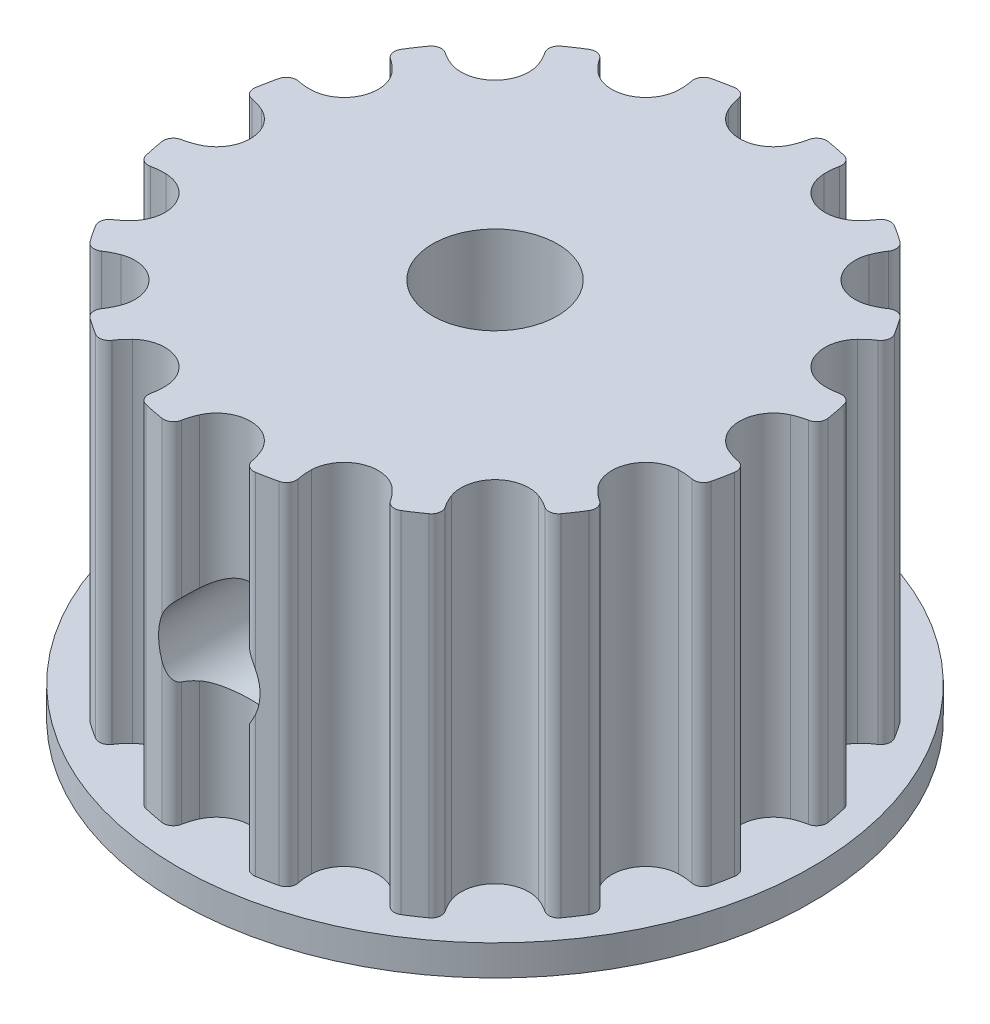
SolidWorks part; units mm, degrees
material "Alum Plate"
ref_plane "Front Plane" through (0, 0, 0) normal (0, 0, 1) x (1, 0, 0)
ref_plane "Top Plane" through (0, 0, 0) normal (0, 1, 0) x (1, 0, 0)
ref_plane "Right Plane" through (0, 0, 0) normal (1, 0, 0) x (0, 0, -1)
other "Bounding Box"
ref_plane "Default Plane" through (-8.9266, -12.7485, 0) normal (-0.1736, 0.9848, 0) x (0.9848, 0.1736, 0)
sketch "Sketch1" plane through (0, 0, 0) normal (0, 1, 0) x (1, 0, 0)
  line L0 (0, -7.8245) -> (0, 0) construction
  circle A0 centre (0, 0) radius 1.5625
  arc B0 (-1.8508, -6.777) -> (-1.6633, -7.0715) centre (-1.6061, -6.8282) ccw
  arc B1 (-1.6633, -7.0715) -> (-1.1695, -7.1697) centre (0, 0) ccw
  arc B2 (-1.1695, -7.1697) -> (-0.8836, -6.9694) centre (-1.1292, -6.923) ccw
  arc B3 (-0.7739, -6.6229) -> (-0.8836, -6.9694) centre (0.61, -7.2516) ccw
  arc B4 (0.7739, -6.6229) -> (-0.7739, -6.6229) centre (0, -6.9745) ccw
  arc B5 (0.8836, -6.9694) -> (0.7739, -6.6229) centre (-0.61, -7.2516) ccw
  arc B6 (0.8836, -6.9694) -> (1.1695, -7.1697) centre (1.1292, -6.923) ccw
  arc B7 (1.1695, -7.1697) -> (1.6633, -7.0715) centre (0, 0) ccw
  arc B8 (1.6633, -7.0715) -> (1.8508, -6.777) centre (1.6061, -6.8282) ccw
  arc B9 (1.8195, -6.4149) -> (1.8508, -6.777) centre (3.3386, -6.4662) ccw
  arc B10 (3.2495, -5.8226) -> (1.8195, -6.4149) centre (2.669, -6.4436) ccw
  arc B11 (3.4834, -6.1008) -> (3.2495, -5.8226) centre (2.2115, -6.9331) ccw
  arc B12 (3.4834, -6.1008) -> (3.8242, -6.1764) centre (3.6926, -5.9639) ccw
  arc B13 (3.8242, -6.1764) -> (4.2428, -5.8967) centre (0, 0) ccw
  arc B14 (4.2428, -5.8967) -> (4.3033, -5.5529) centre (4.0968, -5.6938) ccw
  arc B15 (4.1359, -5.2303) -> (4.3033, -5.5529) centre (5.559, -4.6963) ccw
  arc B16 (5.2303, -4.1359) -> (4.1359, -5.2303) centre (4.9317, -4.9317) ccw
  arc B17 (5.5529, -4.3033) -> (5.2303, -4.1359) centre (4.6963, -5.559) ccw
  arc B18 (5.5529, -4.3033) -> (5.8967, -4.2428) centre (5.6938, -4.0968) ccw
  arc B19 (5.8967, -4.2428) -> (6.1764, -3.8242) centre (0, 0) ccw
  arc B20 (6.1764, -3.8242) -> (6.1008, -3.4834) centre (5.9639, -3.6926) ccw
  arc B21 (5.8226, -3.2495) -> (6.1008, -3.4834) centre (6.9331, -2.2115) ccw
  arc B22 (6.4149, -1.8195) -> (5.8226, -3.2495) centre (6.4436, -2.669) ccw
  arc B23 (6.777, -1.8508) -> (6.4149, -1.8195) centre (6.4662, -3.3386) ccw
  arc B24 (6.777, -1.8508) -> (7.0715, -1.6633) centre (6.8282, -1.6061) ccw
  arc B25 (7.0715, -1.6633) -> (7.1697, -1.1695) centre (0, 0) ccw
  arc B26 (7.1697, -1.1695) -> (6.9694, -0.8836) centre (6.923, -1.1292) ccw
  arc B27 (6.6229, -0.7739) -> (6.9694, -0.8836) centre (7.2516, 0.61) ccw
  arc B28 (6.6229, 0.7739) -> (6.6229, -0.7739) centre (6.9745, 0) ccw
  arc B29 (6.9694, 0.8836) -> (6.6229, 0.7739) centre (7.2516, -0.61) ccw
  arc B30 (6.9694, 0.8836) -> (7.1697, 1.1695) centre (6.923, 1.1292) ccw
  arc B31 (7.1697, 1.1695) -> (7.0715, 1.6633) centre (0, 0) ccw
  arc B32 (7.0715, 1.6633) -> (6.777, 1.8508) centre (6.8282, 1.6061) ccw
  arc B33 (6.4149, 1.8195) -> (6.777, 1.8508) centre (6.4662, 3.3386) ccw
  arc B34 (5.8226, 3.2495) -> (6.4149, 1.8195) centre (6.4436, 2.669) ccw
  arc B35 (6.1008, 3.4834) -> (5.8226, 3.2495) centre (6.9331, 2.2115) ccw
  arc B36 (6.1008, 3.4834) -> (6.1764, 3.8242) centre (5.9639, 3.6926) ccw
  arc B37 (6.1764, 3.8242) -> (5.8967, 4.2428) centre (0, 0) ccw
  arc B38 (5.8967, 4.2428) -> (5.5529, 4.3033) centre (5.6938, 4.0968) ccw
  arc B39 (5.2303, 4.1359) -> (5.5529, 4.3033) centre (4.6963, 5.559) ccw
  arc B40 (4.1359, 5.2303) -> (5.2303, 4.1359) centre (4.9317, 4.9317) ccw
  arc B41 (4.3033, 5.5529) -> (4.1359, 5.2303) centre (5.559, 4.6963) ccw
  arc B42 (4.3033, 5.5529) -> (4.2428, 5.8967) centre (4.0968, 5.6938) ccw
  arc B43 (4.2428, 5.8967) -> (3.8242, 6.1764) centre (0, 0) ccw
  arc B44 (3.8242, 6.1764) -> (3.4834, 6.1008) centre (3.6926, 5.9639) ccw
  arc B45 (3.2495, 5.8226) -> (3.4834, 6.1008) centre (2.2115, 6.9331) ccw
  arc B46 (1.8195, 6.4149) -> (3.2495, 5.8226) centre (2.669, 6.4436) ccw
  arc B47 (1.8508, 6.777) -> (1.8195, 6.4149) centre (3.3386, 6.4662) ccw
  arc B48 (1.8508, 6.777) -> (1.6633, 7.0715) centre (1.6061, 6.8282) ccw
  arc B49 (1.6633, 7.0715) -> (1.1695, 7.1697) centre (0, 0) ccw
  arc B50 (1.1695, 7.1697) -> (0.8836, 6.9694) centre (1.1292, 6.923) ccw
  arc B51 (0.7739, 6.6229) -> (0.8836, 6.9694) centre (-0.61, 7.2516) ccw
  arc B52 (-0.7739, 6.6229) -> (0.7739, 6.6229) centre (0, 6.9745) ccw
  arc B53 (-0.8836, 6.9694) -> (-0.7739, 6.6229) centre (0.61, 7.2516) ccw
  arc B54 (-0.8836, 6.9694) -> (-1.1695, 7.1697) centre (-1.1292, 6.923) ccw
  arc B55 (-1.1695, 7.1697) -> (-1.6633, 7.0715) centre (0, 0) ccw
  arc B56 (-1.6633, 7.0715) -> (-1.8508, 6.777) centre (-1.6061, 6.8282) ccw
  arc B57 (-1.8195, 6.4149) -> (-1.8508, 6.777) centre (-3.3386, 6.4662) ccw
  arc B58 (-3.2495, 5.8226) -> (-1.8195, 6.4149) centre (-2.669, 6.4436) ccw
  arc B59 (-3.4834, 6.1008) -> (-3.2495, 5.8226) centre (-2.2115, 6.9331) ccw
  arc B60 (-3.4834, 6.1008) -> (-3.8242, 6.1764) centre (-3.6926, 5.9639) ccw
  arc B61 (-3.8242, 6.1764) -> (-4.2428, 5.8967) centre (0, 0) ccw
  arc B62 (-4.2428, 5.8967) -> (-4.3033, 5.5529) centre (-4.0968, 5.6938) ccw
  arc B63 (-4.1359, 5.2303) -> (-4.3033, 5.5529) centre (-5.559, 4.6963) ccw
  arc B64 (-5.2303, 4.1359) -> (-4.1359, 5.2303) centre (-4.9317, 4.9317) ccw
  arc B65 (-5.5529, 4.3033) -> (-5.2303, 4.1359) centre (-4.6963, 5.559) ccw
  arc B66 (-5.5529, 4.3033) -> (-5.8967, 4.2428) centre (-5.6938, 4.0968) ccw
  arc B67 (-5.8967, 4.2428) -> (-6.1764, 3.8242) centre (0, 0) ccw
  arc B68 (-6.1764, 3.8242) -> (-6.1008, 3.4834) centre (-5.9639, 3.6926) ccw
  arc B69 (-5.8226, 3.2495) -> (-6.1008, 3.4834) centre (-6.9331, 2.2115) ccw
  arc B70 (-6.4149, 1.8195) -> (-5.8226, 3.2495) centre (-6.4436, 2.669) ccw
  arc B71 (-6.777, 1.8508) -> (-6.4149, 1.8195) centre (-6.4662, 3.3386) ccw
  arc B72 (-6.777, 1.8508) -> (-7.0715, 1.6633) centre (-6.8282, 1.6061) ccw
  arc B73 (-7.0715, 1.6633) -> (-7.1697, 1.1695) centre (0, 0) ccw
  arc B74 (-7.1697, 1.1695) -> (-6.9694, 0.8836) centre (-6.923, 1.1292) ccw
  arc B75 (-6.6229, 0.7739) -> (-6.9694, 0.8836) centre (-7.2516, -0.61) ccw
  arc B76 (-6.6229, -0.7739) -> (-6.6229, 0.7739) centre (-6.9745, 0) ccw
  arc B77 (-6.9694, -0.8836) -> (-6.6229, -0.7739) centre (-7.2516, 0.61) ccw
  arc B78 (-6.9694, -0.8836) -> (-7.1697, -1.1695) centre (-6.923, -1.1292) ccw
  arc B79 (-7.1697, -1.1695) -> (-7.0715, -1.6633) centre (0, 0) ccw
  arc B80 (-7.0715, -1.6633) -> (-6.777, -1.8508) centre (-6.8282, -1.6061) ccw
  arc B81 (-6.4149, -1.8195) -> (-6.777, -1.8508) centre (-6.4662, -3.3386) ccw
  arc B82 (-5.8226, -3.2495) -> (-6.4149, -1.8195) centre (-6.4436, -2.669) ccw
  arc B83 (-6.1008, -3.4834) -> (-5.8226, -3.2495) centre (-6.9331, -2.2115) ccw
  arc B84 (-6.1008, -3.4834) -> (-6.1764, -3.8242) centre (-5.9639, -3.6926) ccw
  arc B85 (-6.1764, -3.8242) -> (-5.8967, -4.2428) centre (0, 0) ccw
  arc B86 (-5.8967, -4.2428) -> (-5.5529, -4.3033) centre (-5.6938, -4.0968) ccw
  arc B87 (-5.2303, -4.1359) -> (-5.5529, -4.3033) centre (-4.6963, -5.559) ccw
  arc B88 (-4.1359, -5.2303) -> (-5.2303, -4.1359) centre (-4.9317, -4.9317) ccw
  arc B89 (-4.3033, -5.5529) -> (-4.1359, -5.2303) centre (-5.559, -4.6963) ccw
  arc B90 (-4.3033, -5.5529) -> (-4.2428, -5.8967) centre (-4.0968, -5.6938) ccw
  arc B91 (-4.2428, -5.8967) -> (-3.8242, -6.1764) centre (0, 0) ccw
  arc B92 (-3.8242, -6.1764) -> (-3.4834, -6.1008) centre (-3.6926, -5.9639) ccw
  arc B93 (-3.2495, -5.8226) -> (-3.4834, -6.1008) centre (-2.2115, -6.9331) ccw
  arc B94 (-1.8195, -6.4149) -> (-3.2495, -5.8226) centre (-2.669, -6.4436) ccw
  arc B95 (-1.8508, -6.777) -> (-1.8195, -6.4149) centre (-3.3386, -6.4662) ccw
  dimension "D1" = 3.125
sketch_block_instance "Block-GT2 16 Tooth Profile-1"
sketch_block "Block-GT2 16 Tooth Profile"
extrude "Boss-Extrude1" add sketch "Sketch1" along normal mid plane 9.525
sketch "Sketch2" plane through (0, -4.7625, 0) normal (0, -1, 0) x (1, 0, 0)
  circle A0 centre (0, 0) radius 7.9375
  circle A1 centre (0, 0) radius 1.5625 construction
  circle A2 centre (0, 0) radius 1.5625
  dimension "D1" = 15.875
extrude "Boss-Extrude2" add sketch "Sketch2" against normal blind 0.762
sketch "Sketch4" [suppressed] plane through (0, -4.7625, 0) normal (0, -1, 0) x (1, 0, 0)
  circle A0 centre (-3.81, 0) radius 1.25
  circle A1 centre (3.81, 0) radius 1.25
  dimension "D1" = 2.5
extrude "Cut-Extrude2" [suppressed] cut sketch "Sketch4" against normal through all
chamfer "Chamfer1" [suppressed] distance 0.254 angle 45
sketch "Sketch5" plane through (0, 0, 0) normal (0, 0, 1) x (1, 0, 0)
  circle A0 centre (0, 0) radius 1.27
  dimension "D1" = 2.54
extrude "Cut-Extrude3" cut sketch "Sketch5" against normal through all both and the other way through all
